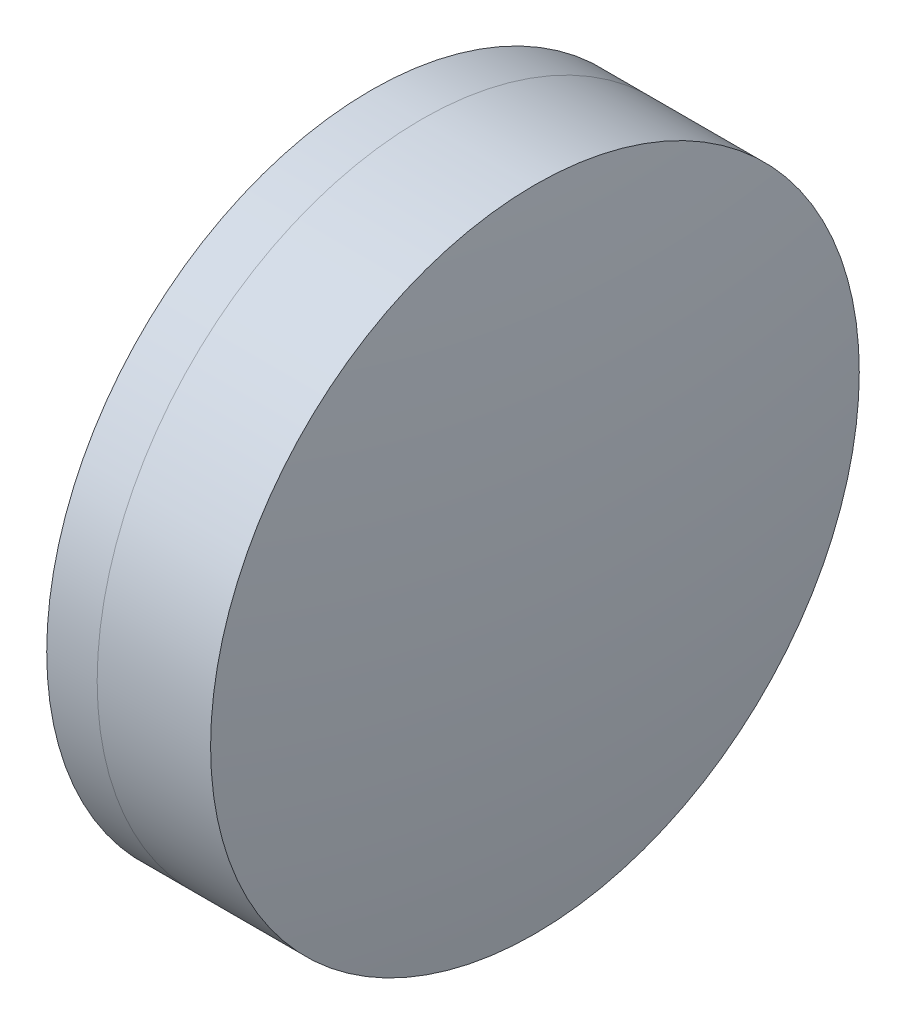
SolidWorks part; units mm, degrees
ref_plane "前视基准面" through (0, 0, 0) normal (0, 0, 1) x (1, 0, 0)
ref_plane "上视基准面" through (0, 0, 0) normal (0, 1, 0) x (1, 0, 0)
ref_plane "右视基准面" through (0, 0, 0) normal (1, 0, 0) x (0, 0, -1)
sketch "草图1" plane through (0, 0, 0) normal (0, 1, 0) x (1, 0, 0)
  line L0 (-9.7026, 0) -> (52.5896, 0) construction
  line L1 (39.6186, -12.5) -> (41.5629, -12.5)
  line L2 (39.6186, 12.5) -> (41.5629, 12.5)
  arc A0 (41.5629, -12.5) -> (41.5629, 12.5) centre (14.8797, 0) ccw
  arc A1 (39.6186, 12.5) -> (39.6186, -12.5) centre (78.4377, 0) ccw
  point P4 (52.5896, 0)
  point P10 (37.6557, 0)
  point P11 (44.3457, 0)
  dimension "D3" = 40.782
  dimension "D4" = 29.466
  dimension "D1" = 12.5
  dimension "D2" = 12.5
  dimension "D5" = 6.69
revolve "旋转1" add sketch "草图1" angle 360 about L0
sketch "草图2" plane through (0, 0, 0) normal (0, 1, 0) x (1, 0, 0)
  line L0 (-0.5519, 0) -> (47.7152, 0) construction
  line L2 (41.5629, 12.5) -> (45.9338, 12.5)
  line L3 (41.5629, -12.5) -> (45.9338, -12.5)
  arc A0 (45.9338, -12.5) -> (45.9338, 12.5) centre (-37.4403, 0) ccw
  arc A1 (41.5629, -12.5) -> (41.5629, 12.5) centre (14.8797, 0) ccw construction
  arc A2 (41.5629, -12.5) -> (41.5629, 12.5) centre (14.8797, 0) ccw
  point P4 (44.3457, 0)
  point P8 (46.8657, 0)
  dimension "D1" = 84.306
  dimension "D2" = 2.52
revolve "旋转3" add sketch "草图2" angle 360 about L0
